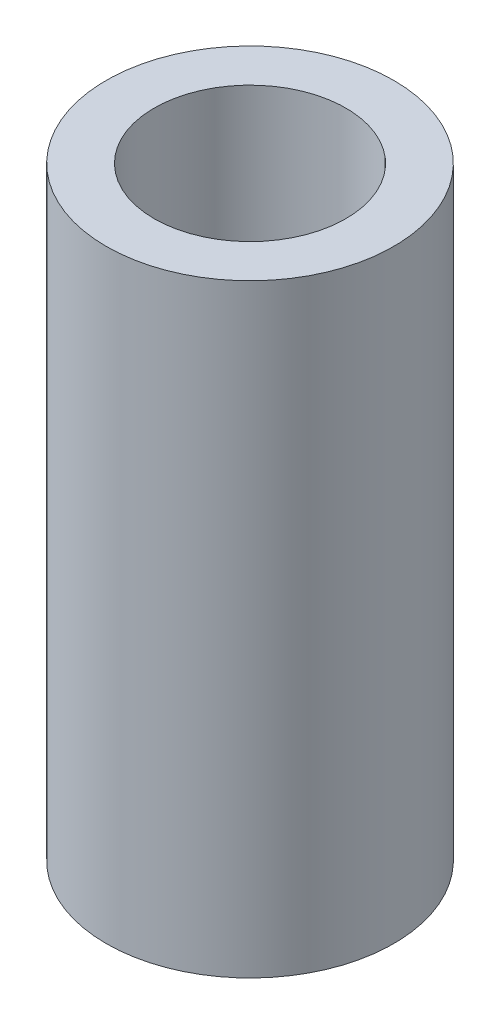
SolidWorks part; units mm, degrees
material "Silicon Rubber"
ref_plane "Front Plane" through (0, 0, 0) normal (0, 0, 1) x (1, 0, 0)
ref_plane "Top Plane" through (0, 0, 0) normal (0, 1, 0) x (1, 0, 0)
ref_plane "Right Plane" through (0, 0, 0) normal (1, 0, 0) x (0, 0, -1)
sketch "Sketch2" plane through (0, 0, 0) normal (0, 1, 0) x (1, 0, 0)
  line L0 (0, 2.5) -> (0, 8) construction
  line L1 (-17.5, 0) -> (17.5, 0) construction
  circle A0 centre (0, 0) radius 17.5 construction
  circle A1 centre (0, 0) radius 2.5 construction
  circle A2 centre (0, 8) radius 3.175
  circle A3 centre (0, 8) radius 4.7625
  circle A4 centre (0, -8) radius 3.175 construction
  circle A5 centre (0, -8) radius 4.7625 construction
  dimension "D1" = 35
  dimension "D2" = 5
  dimension "D4" = 6.35
  dimension "D5" = 9.525
  dimension "D3" = 5.5
sketch "Sketch4" plane through (0, 0, 0) normal (1, 0, 0) x (0, 0, -1)
  line L0 (8, 0) -> (8, 20)
  dimension "D1" = 20
sweep "Sweep2" add profiles "Sketch2" path "Sketch4"
ref_plane "Plane2" through (0, -10, 0) normal (0, 1, 0) x (1, 0, 0)
